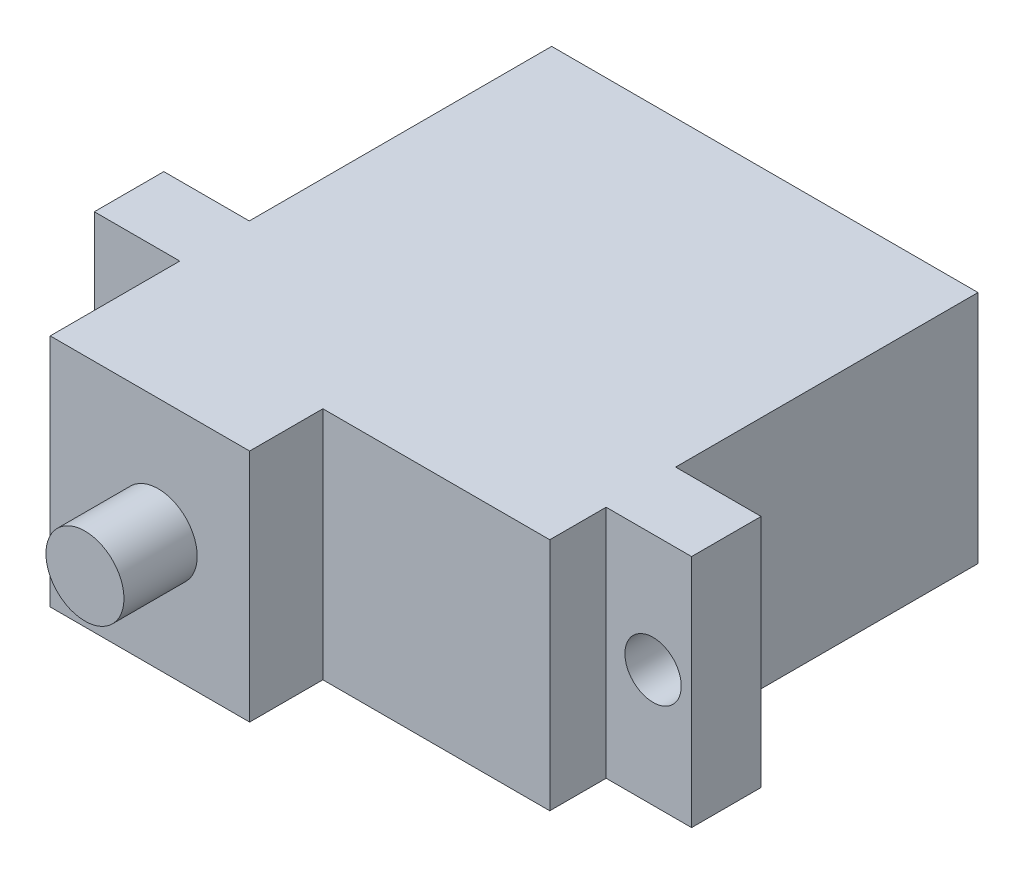
SolidWorks part; units mm, degrees
ref_plane "Front Plane" through (0, 0, 0) normal (0, 0, 1) x (1, 0, 0)
ref_plane "Top Plane" through (0, 0, 0) normal (0, 1, 0) x (1, 0, 0)
ref_plane "Right Plane" through (0, 0, 0) normal (1, 0, 0) x (0, 0, -1)
sketch "Sketch1" plane through (0, 0, 0) normal (0, 0, 1) x (1, 0, 0)
  line L1 (-11.35, 6.25) -> (11.35, 6.25)
  line L2 (-11.35, 6.25) -> (-11.35, -6.25)
  line L3 (-11.35, -6.25) -> (11.35, -6.25)
  line L4 (11.35, 6.25) -> (11.35, -6.25)
  line L5 (-11.35, 6.25) -> (11.35, -6.25) construction
  line L6 (-11.35, -6.25) -> (11.35, 6.25) construction
  point P0 (0, 0)
  dimension "D1" = 12.5
  dimension "D2" = 22.7
extrude "Boss-Extrude1" add sketch "Sketch1" along normal blind 22.8
sketch "Sketch2" plane through (0, 0, 22.8) normal (0, 0, 1) x (1, 0, 0)
  line L1 (-15.9, 6.25) -> (15.9, 6.25)
  line L2 (-15.9, 6.25) -> (-15.9, -6.25)
  line L3 (-15.9, -6.25) -> (15.9, -6.25)
  line L4 (11.35, -6.25) -> (11.35, 6.25)
  line L5 (11.35, 6.25) -> (-11.35, 6.25)
  line L6 (-11.35, 6.25) -> (-11.35, -6.25)
  line L7 (-11.35, -6.25) -> (11.35, -6.25)
  line L8 (11.35, -6.25) -> (11.35, 6.25)
  line L9 (11.35, 6.25) -> (-11.35, 6.25)
  line L10 (-11.35, 6.25) -> (-11.35, -6.25)
  line L11 (-11.35, -6.25) -> (11.35, -6.25)
  line L12 (15.9, 6.25) -> (15.9, -6.25)
  line L13 (-15.9, 6.25) -> (15.9, -6.25) construction
  line L14 (-15.9, -6.25) -> (15.9, 6.25) construction
  point P2 (0, 0)
  line M9 (11.35, -6.25) -> (11.35, 6.25)
  line M11 (-11.35, 6.25) -> (-11.35, -6.25)
  dimension "D2" = 31.8
  dimension "D1" = 0
extrude "Boss-Extrude2" add sketch "Sketch2" against normal offset from surface (6.7 mm away) 16.1 contours L2 L3 L1 M11 | L12 L1 L3 M9 up to face at (0, 0, 0)
sketch "Sketch3" plane through (0, -6.25, 0) normal (0, -1, 0) x (1, 0, 0)
  line L1 (-15.9, 22.8) -> (-11.35, 22.8)
  line L2 (-15.9, 22.8) -> (-15.9, 19.8)
  line L3 (-15.9, 19.8) -> (-11.35, 19.8)
  line L4 (-11.35, 22.8) -> (-11.35, 19.8)
  line L5 (0, 0) -> (0, 4.9471) construction
  line L6 (11.35, 22.8) -> (11.35, 19.8)
  line L7 (15.9, 19.8) -> (11.35, 19.8)
  line L8 (15.9, 22.8) -> (15.9, 19.8)
  line L9 (15.9, 22.8) -> (11.35, 22.8)
  dimension "D1" = 3
extrude "Cut-Extrude1" cut sketch "Sketch3" against normal through all
sketch "Sketch4" plane through (0, 0, 19.8) normal (0, 0, 1) x (1, 0, 0)
  line L0 (0, 0) -> (0, -8.5487) construction
  circle A0 centre (13.85, 0) radius 1.5
  circle A1 centre (-13.85, 0) radius 1.5
  dimension "D2" = 3
  dimension "D1" = 27.7
extrude "Cut-Extrude2" cut sketch "Sketch4" against normal blind 16.1
sketch "Sketch6" plane through (0, 0, 22.8) normal (0, 0, 1) x (1, 0, 0)
  line L0 (-11.35, -6.25) -> (11.35, -6.25) construction
  line L1 (-11.35, 6.25) -> (-0.7313, 6.25)
  line L2 (-11.35, 6.25) -> (-11.35, -6.25)
  line L3 (-11.35, -6.25) -> (-0.7313, -6.25)
  line L4 (-0.7313, 6.25) -> (-0.7313, -6.25)
extrude "Boss-Extrude4" add sketch "Sketch6" along normal blind 3.9
sketch "Sketch8" plane through (0, 0, 26.7) normal (0, 0, 1) x (1, 0, 0)
  line L0 (-11.35, 6.25) -> (-11.35, -6.25) construction
  circle A0 centre (-5.6, 0) radius 2.0776
  dimension "D1" = 5.75
extrude "Boss-Extrude5" add sketch "Sketch8" along normal blind 3.9
